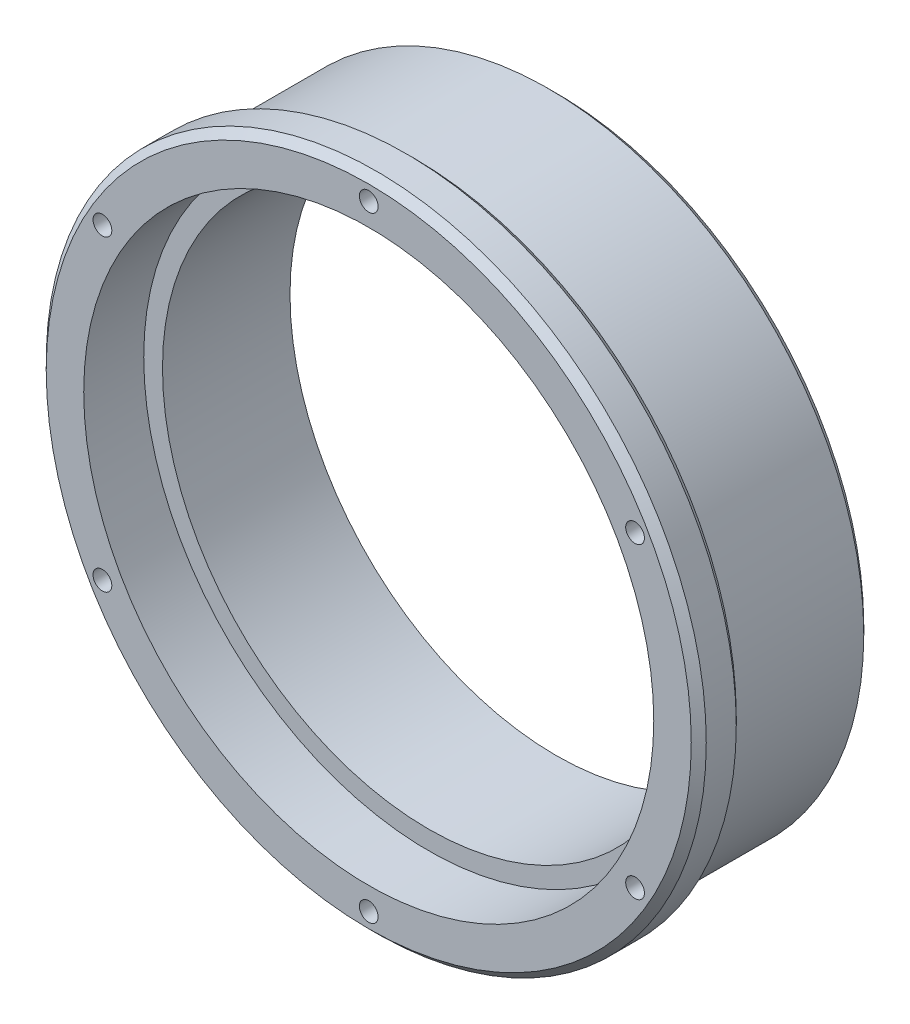
SolidWorks part; units mm, degrees
material "6061 合金"
ref_plane "前视基准面" through (0, 0, 0) normal (0, 0, 1) x (1, 0, 0)
ref_plane "上视基准面" through (0, 0, 0) normal (0, 1, 0) x (1, 0, 0)
ref_plane "右视基准面" through (0, 0, 0) normal (1, 0, 0) x (0, 0, -1)
sketch "草图1" plane through (0, 0, 0) normal (0, 0, 1) x (1, 0, 0)
  circle A0 centre (0, 0) radius 42
  circle A1 centre (0, 0) radius 35.5
  dimension "D1" = 71
  dimension "D2" = 84
extrude "凸台-拉伸1" add sketch "草图1" along normal blind 25
sketch "草图2" plane through (0, 0, 25) normal (0, 0, 1) x (1, 0, 0)
  circle A0 centre (0, 0) radius 38
  dimension "D1" = 76
extrude "切除-拉伸1" cut sketch "草图2" against normal blind 8
sketch "草图3" plane through (0, 0, 0) normal (0, 0, -1) x (-1, 0, 0)
  circle A0 centre (0, 0) radius 38.5 construction
  circle A1 centre (0, 38.5) radius 1.25 construction
  circle A2 centre (33.342, 19.25) radius 1.25 construction
  circle A3 centre (33.342, -19.25) radius 1.25 construction
  circle A4 centre (0, -38.5) radius 1.25 construction
  circle A5 centre (-33.342, -19.25) radius 1.25 construction
  circle A6 centre (-33.342, 19.25) radius 1.25 construction
  point P6 (0, 38.5)
  point P7 (33.342, 19.25)
  point P18 (0, 0)
  point P19 (33.342, -19.25)
  point P20 (0, -38.5)
  point P21 (-33.342, -19.25)
  point P22 (-33.342, 19.25)
  dimension "D1" = 77
  dimension "D2" = 2.5
  dimension "D3" = 6
hole_wizard "M3 螺纹孔1" positions "3D草图1" profile "草图5" tap size "M3" standard "GB"
sketch3d "3D草图1"
  point P0 (-33.342, 19.25, 0)
  point P3 (-33.342, -19.25, 0)
  point P6 (0, -38.5, 0)
  point P9 (33.342, -19.25, 0)
  point P12 (33.342, 19.25, 0)
  point P15 (0, 38.5, 0)
sketch "草图5" plane through (-33.342, 19.25, 0) normal (1, 0, 0) x (0, 1, 0)
  line L0 (0, 0) -> (0, 6.7511)
  line L1 (0, 6.7511) -> (1.25, 6)
  line L2 (1.25, 6) -> (1.25, 0)
  line L5 (1.25, 0) -> (0, 0)
  line L10 (0, 6.7511) -> (-1.25, 6) construction
  line L11 (0, -6.35) -> (0, 107.95) construction
  dimension "螺纹孔钻头直径" = 2.5
  dimension "螺纹孔钻头深度" = 6
  dimension "导头角度" = 118
cosmetic thread "孔螺蚊线1" parameters "D1"=6, "D2"=3
cosmetic thread "孔螺蚊线2" parameters "D1"=6, "D2"=3
cosmetic thread "孔螺蚊线3" parameters "D1"=6, "D2"=3
cosmetic thread "孔螺蚊线4" parameters "D1"=6, "D2"=3
cosmetic thread "孔螺蚊线5" parameters "D1"=6, "D2"=3
cosmetic thread "孔螺蚊线6" parameters "D1"=6, "D2"=3
sketch "草图4" plane through (0, 0, 25) normal (0, 0, 1) x (1, 0, 0)
  circle A0 centre (0, 0) radius 40 construction
  circle A1 centre (0, 40) radius 1.25 construction
  circle A2 centre (34.641, 20) radius 1.25 construction
  circle A3 centre (34.641, -20) radius 1.25 construction
  circle A4 centre (0, -40) radius 1.25 construction
  circle A5 centre (-34.641, -20) radius 1.25 construction
  circle A6 centre (-34.641, 20) radius 1.25 construction
  point P18 (0, 0)
  dimension "D1" = 80
  dimension "D2" = 2.5
  dimension "D3" = 6
sketch "草图10" plane through (0, 0, 25) normal (0, 0, 1) x (1, 0, 0)
  circle A0 centre (0, 0) radius 42
  circle A1 centre (0, 0) radius 44
  circle A2 centre (0, 0) radius 42 construction
  dimension "D1" = 2
extrude "凸台-拉伸2" add sketch "草图10" against normal blind 6
chamfer "倒角1" distance 1 angle 45 1 edges at (42, 0, 0)
sketch "草图7" plane through (0, 0, 25) normal (0, 0, 1) x (1, 0, 0)
  circle A0 centre (0, 0) radius 41 construction
  point P3 (0, 41)
  point P7 (35.507, 20.5)
  point P8 (35.507, -20.5)
  point P9 (0, -41)
  point P10 (-35.507, -20.5)
  point P11 (-35.507, 20.5)
  point P12 (0, 0)
  dimension "D1" = 82
  dimension "D2" = 6
hole_wizard "M3 螺纹孔3" positions "3D草图2" profile "草图11" tap size "M3" standard "GB"
sketch3d "3D草图2"
  point P0 (35.507, 20.5, 25)
  point P3 (35.507, -20.5, 25)
  point P6 (0, 41, 25)
  point P9 (0, -41, 25)
  point P12 (-35.507, -20.5, 25)
  point P15 (-35.507, 20.5, 25)
  point P20 (84.6166, -20.4705, 0)
sketch "草图11" plane through (35.507, 20.5, 25) normal (1, 0, 0) x (0, -1, 0)
  line L0 (0, 0) -> (0, 5.7511)
  line L1 (0, 5.7511) -> (1.25, 5)
  line L2 (1.25, 5) -> (1.25, 0)
  line L5 (1.25, 0) -> (0, 0)
  line L10 (0, 5.7511) -> (-1.25, 5) construction
  line L11 (0, -6.35) -> (0, 107.95) construction
  dimension "螺纹孔钻头直径" = 2.5
  dimension "螺纹孔钻头深度" = 5
  dimension "导头角度" = 118
cosmetic thread "孔螺蚊线7" parameters "D1"=5, "D2"=3
cosmetic thread "孔螺蚊线8" parameters "D1"=5, "D2"=3
cosmetic thread "孔螺蚊线9" parameters "D1"=5, "D2"=3
cosmetic thread "孔螺蚊线10" parameters "D1"=5, "D2"=3
cosmetic thread "孔螺蚊线11" parameters "D1"=5, "D2"=3
cosmetic thread "孔螺蚊线13" parameters "D1"=5, "D2"=3
chamfer "倒角2" distance 1 angle 45 2 edges at (44, 0, 19) (44, 0, 25)
